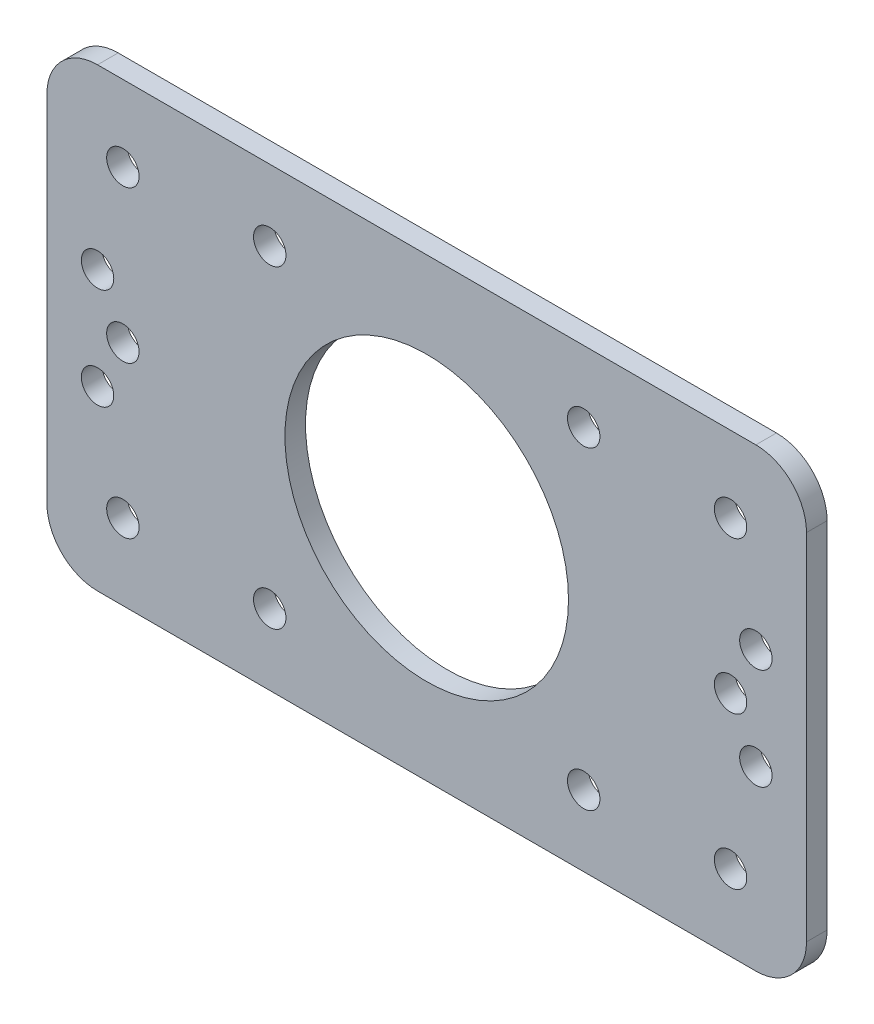
SolidWorks part; units mm, degrees
ref_plane "Front Plane" through (0, 0, 0) normal (0, 0, 1) x (1, 0, 0)
ref_plane "Top Plane" through (0, 0, 0) normal (0, 1, 0) x (1, 0, 0)
ref_plane "Right Plane" through (0, 0, 0) normal (1, 0, 0) x (0, 0, -1)
sketch "Sketch1" plane through (0, 0, 0) normal (0, 0, 1) x (1, 0, 0)
  line L0 (22.5, 22.5) -> (22.5, -22.5) construction
  line L1 (-37.5, -22.5) -> (37.5, -22.5)
  line L2 (-37.5, -22.5) -> (-37.5, 22.5)
  line L3 (-37.5, 22.5) -> (37.5, 22.5)
  line L4 (37.5, -22.5) -> (37.5, 22.5)
  line L5 (-37.5, -22.5) -> (37.5, 22.5) construction
  line L6 (-37.5, 22.5) -> (37.5, -22.5) construction
  line L7 (-15.5, -15.5) -> (15.5, -15.5) construction
  line L8 (-15.5, -15.5) -> (-15.5, 15.5) construction
  line L9 (-15.5, 15.5) -> (15.5, 15.5) construction
  line L10 (15.5, -15.5) -> (15.5, 15.5) construction
  line L11 (-15.5, -15.5) -> (15.5, 15.5) construction
  line L12 (-15.5, 15.5) -> (15.5, -15.5) construction
  line L13 (-22.5, 22.5) -> (-22.5, -22.5) construction
  circle A0 centre (0, 0) radius 14
  circle A1 centre (-15.5, 15.5) radius 1.6
  circle A2 centre (15.5, 15.5) radius 1.6
  circle A3 centre (15.5, -15.5) radius 1.6
  circle A4 centre (-15.5, -15.5) radius 1.6
  point P0 (0, 0)
  dimension "D2" = 28
  dimension "D3" = 3.2
  dimension "D1" = 31
  dimension "D4" = 45
  dimension "D5" = 75
  dimension "D6" = 15
  dimension "D7" = 15
extrude "Boss-Extrude1" add sketch "Sketch1" along normal blind 2.032
fillet "Fillet2" radius 5 4 edges at (37.5, 22.5, 1.016) (37.5, -22.5, 1.016) (-37.5, -22.5, 1.016) (-37.5, 22.5, 1.016)
sketch "Sketch2" plane through (0, 0, 2.032) normal (0, 0, 1) x (1, 0, 0)
  line L0 (0, 40.4519) -> (0, -37.5654) construction
  line L1 (0, -54.6431) -> (0, 54.6431) construction
  line L2 (47.3483, 0) -> (-47.3483, 0) construction
  line L3 (55, 0) -> (-55, 0) construction
  line L4 (-37.5, 17.5) -> (-37.5, -17.5) construction
  circle A0 centre (-30, 0) radius 1.6
  circle A1 centre (-30, 15) radius 1.6
  circle A2 centre (-30, -15) radius 1.6
  circle A3 centre (30, -15) radius 1.6
  circle A4 centre (30, 15) radius 1.6
  circle A5 centre (30, 0) radius 1.6
  dimension "D1" = 3.2
  dimension "D2" = 7.5
  dimension "D3" = 15
extrude "Cut-Extrude1" cut sketch "Sketch2" against normal through all
sketch "Sketch3" plane through (0, 0, 0) normal (0, 0, -1) x (-1, 0, 0)
  line L0 (-43.1144, 0) -> (46.045, 0) construction
  line L1 (0, 27.0792) -> (0, -27.3033) construction
  line L2 (-37.5, -17.5) -> (-37.5, 17.5) construction
  circle A0 centre (-32.5, 5) radius 1.6
  circle A1 centre (-32.5, -5) radius 1.6
  circle A2 centre (32.5, -5) radius 1.6
  circle A3 centre (32.5, 5) radius 1.6
  circle A4 centre (-30, -15) radius 1.6 construction
  point P15 (-30, -15)
  point P16 (-30, 15)
  dimension "D1" = 3.2
  dimension "D2" = 5
  dimension "D3" = 10
extrude "Cut-Extrude2" cut sketch "Sketch3" against normal through all
sketch "Alignment Sketch 1" plane through (0, 0, 2.032) normal (0, 0, 1) x (1, 0, 0)
  line L0 (-30, 15) -> (-30, -15) construction
  line L1 (30, 15) -> (30, -15) construction
  circle A0 centre (30, 15) radius 1.6 construction
  point P0 (-30, 15)
  point P1 (-30, 0)
  point P3 (-30, -15)
  point P5 (30, 15)
  point P7 (30, 0)
  point P8 (30, -15)
